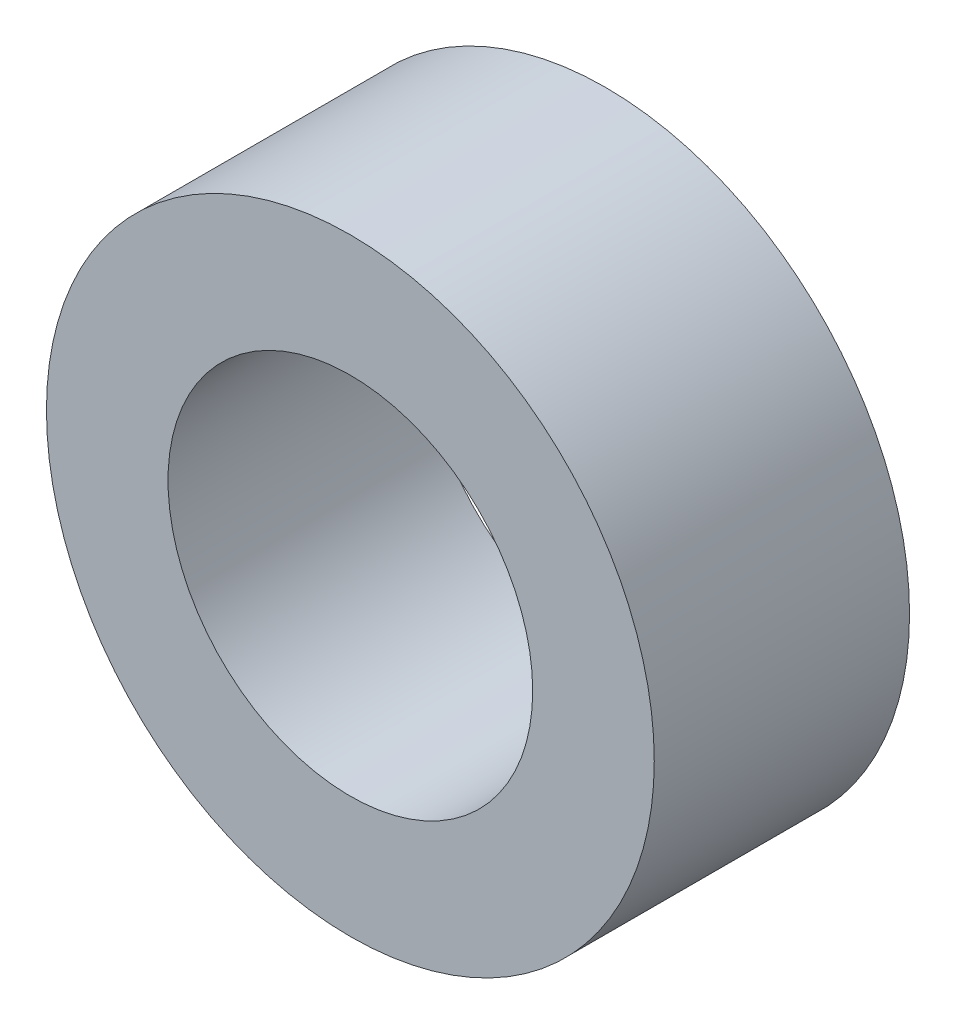
SolidWorks part; units mm, degrees
ref_plane "前视基准面" through (0, 0, 0) normal (0, 0, 1) x (1, 0, 0)
ref_plane "上视基准面" through (0, 0, 0) normal (0, 1, 0) x (1, 0, 0)
ref_plane "右视基准面" through (0, 0, 0) normal (1, 0, 0) x (0, 0, -1)
sketch "草图1" plane through (0, 0, 0) normal (0, 0, 1) x (1, 0, 0)
  circle A0 centre (0, 0) radius 1.5
  circle A1 centre (0, 0) radius 2.5
  dimension "D1" = 3
  dimension "D2" = 5
extrude "凸台-拉伸1" add sketch "草图1" along normal blind 2.1
